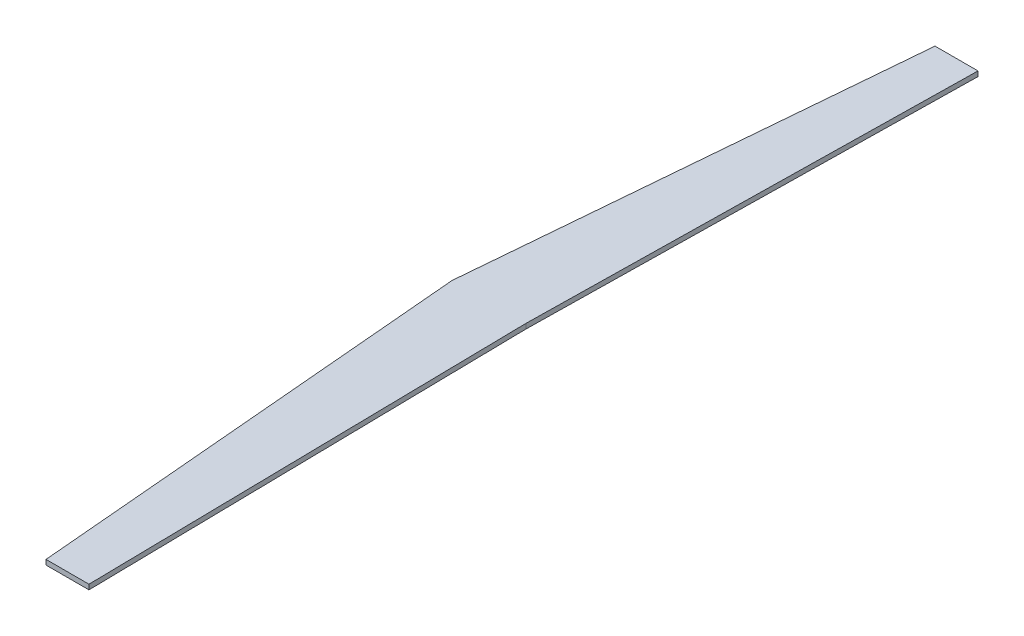
SolidWorks part; units mm, degrees
material "ABS"
ref_plane "Front Plane" through (0, 0, 0) normal (0, 0, 1) x (1, 0, 0)
ref_plane "Top Plane" through (0, 0, 0) normal (0, 1, 0) x (1, 0, 0)
ref_plane "Right Plane" through (0, 0, 0) normal (1, 0, 0) x (0, 0, -1)
sketch "Sketch1" plane through (0, 0, 0) normal (0, 1, 0) x (1, 0, 0)
  line L0 (45, 0) -> (50, -300) construction
  line L1 (50, -300) -> (-30, -300) construction
  line L2 (-30, -300) -> (-74.7411, 0) construction
  line L3 (-74.7411, 0) -> (-30, 300) construction
  line L4 (-30, 300) -> (50, 300) construction
  line L5 (50, 300) -> (45, 0) construction
  line L6 (45, 0) -> (-74.7411, 0) construction
  line L7 (45, 0) -> (0, 0) construction
  line L8 (50, 300) -> (26, 300) construction
  line L9 (50, -300) -> (26, -300) construction
  line L10 (26, -300) -> (0, 0) construction
  line L11 (0, 0) -> (26, 300) construction
  line L12 (49.5, 270) -> (23.4, 270)
  line L13 (23.4, -270) -> (49.5, -270)
  line L14 (49.5, -270) -> (45, 0)
  line L15 (45, 0) -> (49.5, 270)
  line L16 (23.4, 270) -> (0, 0)
  line L17 (0, 0) -> (23.4, -270)
  dimension "D1" = 45
  dimension "D2" = 24
  dimension "D3" = 30
  dimension "D4" = 30
  dimension "D5" = 24
extrude "Boss-Extrude1" add sketch "Sketch1" along normal blind 3
